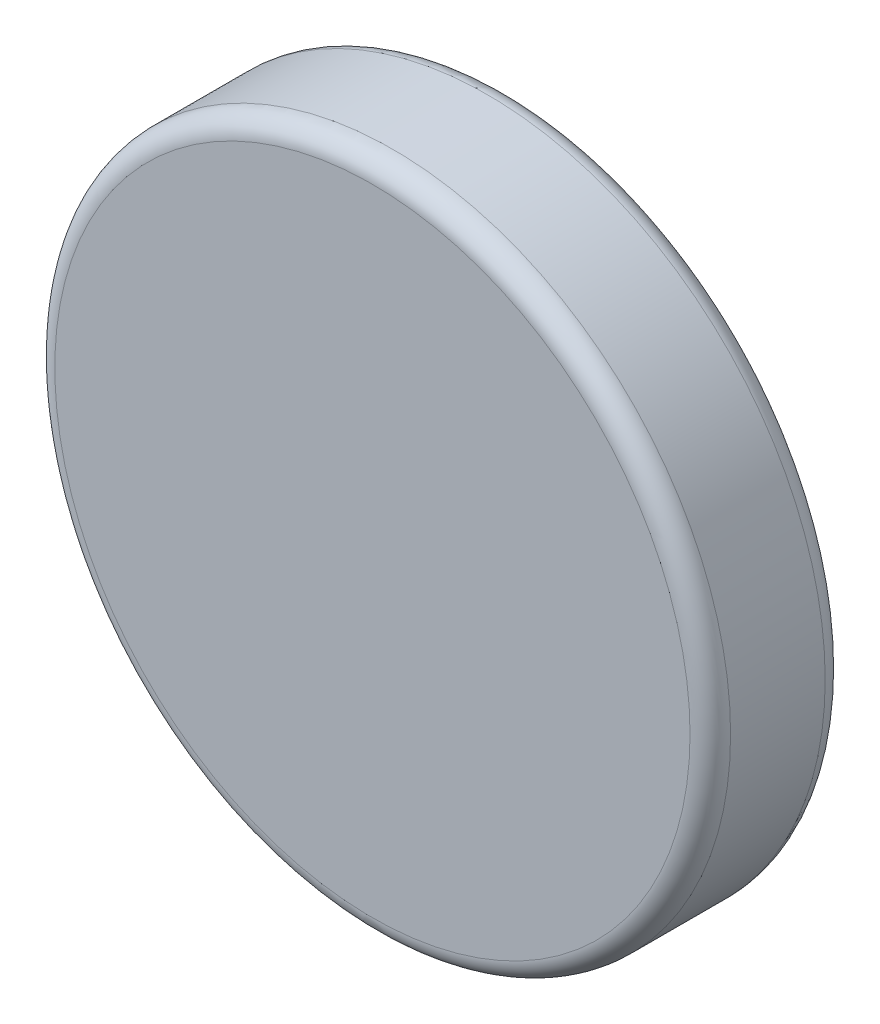
SolidWorks part; units mm, degrees
ref_plane "Plan de face" through (0, 0, 0) normal (0, 0, 1) x (1, 0, 0)
ref_plane "Plan de dessus" through (0, 0, 0) normal (0, 1, 0) x (1, 0, 0)
ref_plane "Plan de droite" through (0, 0, 0) normal (1, 0, 0) x (0, 0, -1)
sketch "Esquisse1" plane through (0, 0, 0) normal (0, 0, 1) x (1, 0, 0)
  circle A0 centre (0, 0) radius 5
  dimension "D1" = 10
extrude "Boss.-Extru.1" add sketch "Esquisse1" along normal blind 2
fillet "Congé1" radius 0.3 2 edges at (5, 0, 0) (5, 0, 2)
